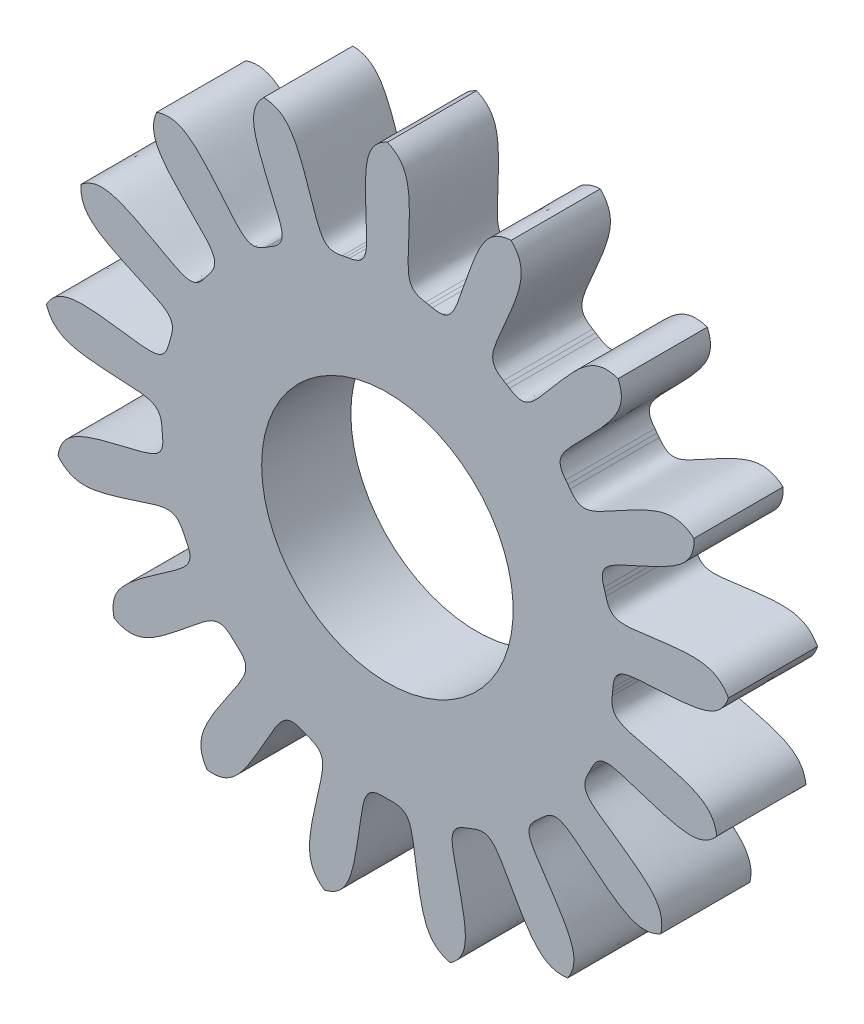
SolidWorks part; units mm, degrees
ref_plane "Alzado" through (0, 0, 0) normal (0, 0, 1) x (1, 0, 0)
ref_plane "Planta" through (0, 0, 0) normal (0, 1, 0) x (1, 0, 0)
ref_plane "Vista lateral" through (0, 0, 0) normal (1, 0, 0) x (0, 0, -1)
sketch "Sketch1" plane through (0, 0, 0) normal (0, 0, 1) x (1, 0, 0)
  line L0 (0, -1000) -> (0, 49000) construction
  line L1 (0, 0) -> (0.6543, 3.5) construction
  line L2 (0.2133, 1.2499) -> (0.233, 1.2464)
  line L3 (-0.2133, 1.2499) -> (-0.233, 1.2464)
  line L4 (0.2526, 1.2426) -> (0.233, 1.2464)
  line L5 (0.6504, 1.0885) -> (0.6675, 1.0781)
  line L6 (0.6844, 1.0674) -> (0.6675, 1.0781)
  line L7 (0.9997, 0.78) -> (1.0119, 0.7641)
  line L8 (1.0238, 0.7481) -> (1.0119, 0.7641)
  line L9 (1.214, 0.3662) -> (1.2196, 0.347)
  line L10 (1.2249, 0.3277) -> (1.2196, 0.347)
  line L11 (1.2643, -0.0971) -> (1.2626, -0.117)
  line L12 (1.2606, -0.1369) -> (1.2626, -0.117)
  line L13 (1.1438, -0.5472) -> (1.1351, -0.5652)
  line L14 (1.126, -0.583) -> (1.1351, -0.5652)
  line L15 (0.8689, -0.9235) -> (0.8542, -0.9371)
  line L16 (0.8394, -0.9504) -> (0.8542, -0.9371)
  line L17 (0.4766, -1.175) -> (0.4581, -1.1824)
  line L18 (0.4393, -1.1895) -> (0.4581, -1.1824)
  line L19 (0.02, -1.2678) -> (0, -1.268)
  line L20 (-0.02, -1.2678) -> (0, -1.268)
  line L21 (-0.4393, -1.1895) -> (-0.4581, -1.1824)
  line L22 (-0.4766, -1.175) -> (-0.4581, -1.1824)
  line L23 (-0.8394, -0.9504) -> (-0.8542, -0.9371)
  line L24 (-0.8689, -0.9235) -> (-0.8542, -0.9371)
  line L25 (-1.126, -0.583) -> (-1.1351, -0.5652)
  line L26 (-1.1438, -0.5472) -> (-1.1351, -0.5652)
  line L27 (-1.2606, -0.1369) -> (-1.2626, -0.117)
  line L28 (-1.2643, -0.0971) -> (-1.2626, -0.117)
  line L29 (-1.2249, 0.3277) -> (-1.2196, 0.347)
  line L30 (-1.214, 0.3662) -> (-1.2196, 0.347)
  line L31 (-1.0238, 0.7481) -> (-1.0119, 0.7641)
  line L32 (-0.9997, 0.78) -> (-1.0119, 0.7641)
  line L33 (-0.6844, 1.0674) -> (-0.6675, 1.0781)
  line L34 (-0.6504, 1.0885) -> (-0.6675, 1.0781)
  line L35 (-0.2526, 1.2426) -> (-0.233, 1.2464)
  circle A0 centre (0, 0) radius 1.92 construction
  circle A1 centre (0, 0) radius 1.268 construction
  spline S0 degree 3 poles (0, 1.92) (0.1051, 1.8729) (0.1297, 1.764) (0.1133, 1.3379) (0.1067, 1.2671) (0.2133, 1.2499) knots 0 0 0 0 0.42728 0.52728 1 1 1 1
  spline S1 degree 3 poles (0, 1.92) (-0.1051, 1.8729) (-0.1297, 1.764) (-0.1133, 1.3379) (-0.1067, 1.2671) (-0.2133, 1.2499) knots 0 0 0 0 0.42728 0.52728 1 1 1 1
  spline S2 degree 3 poles (0.6936, 1.7903) (0.5786, 1.7844) (0.5163, 1.6917) (0.3776, 1.2885) (0.3583, 1.2201) (0.2526, 1.2426) knots 0 0 0 0 0.42728 0.52728 1 1 1 1
  spline S3 degree 3 poles (0.6936, 1.7903) (0.7746, 1.7084) (0.7581, 1.598) (0.589, 1.2066) (0.5572, 1.143) (0.6504, 1.0885) knots 0 0 0 0 0.42728 0.52728 1 1 1 1
  spline S4 degree 3 poles (1.2935, 1.4189) (1.1841, 1.4549) (1.0926, 1.391) (0.8175, 1.065) (0.7748, 1.0083) (0.6844, 1.0674) knots 0 0 0 0 0.42728 0.52728 1 1 1 1
  spline S5 degree 3 poles (1.2935, 1.4189) (1.3394, 1.3133) (1.2842, 1.2163) (0.9851, 0.9123) (0.9325, 0.8646) (0.9997, 0.78) knots 0 0 0 0 0.42728 0.52728 1 1 1 1
  spline S6 degree 3 poles (1.7187, 0.8558) (1.6297, 0.9289) (1.5213, 0.9023) (1.1471, 0.6978) (1.0867, 0.6603) (1.0238, 0.7481) knots 0 0 0 0 0.42728 0.52728 1 1 1 1
  spline S7 degree 3 poles (1.7187, 0.8558) (1.7234, 0.7407) (1.6369, 0.6702) (1.2481, 0.4949) (1.1819, 0.4693) (1.214, 0.3662) knots 0 0 0 0 0.42728 0.52728 1 1 1 1
  spline S8 degree 3 poles (1.9118, 0.1772) (1.8552, 0.2775) (1.7445, 0.2919) (1.3217, 0.2363) (1.2519, 0.2232) (1.2249, 0.3277) knots 0 0 0 0 0.42728 0.52728 1 1 1 1
  spline S9 degree 3 poles (1.9118, 0.1772) (1.8746, 0.0682) (1.7684, 0.0337) (1.3426, 0.0106) (1.2716, 0.0107) (1.2643, -0.0971) knots 0 0 0 0 0.42728 0.52728 1 1 1 1
  spline S10 degree 3 poles (1.8467, -0.5254) (1.8301, -0.4115) (1.7321, -0.358) (1.3178, -0.2571) (1.248, -0.2441) (1.2606, -0.1369) knots 0 0 0 0 0.42728 0.52728 1 1 1 1
  spline S11 degree 3 poles (1.8467, -0.5254) (1.7726, -0.6136) (1.6612, -0.6074) (1.2558, -0.4751) (1.1896, -0.4494) (1.1438, -0.5472) knots 0 0 0 0 0.42728 0.52728 1 1 1 1
  spline S12 degree 3 poles (1.5322, -1.1571) (1.5579, -1.0448) (1.4858, -0.9596) (1.1359, -0.7158) (1.0755, -0.6785) (1.126, -0.583) knots 0 0 0 0 0.42728 0.52728 1 1 1 1
  spline S13 degree 3 poles (1.5322, -1.1571) (1.4312, -1.2125) (1.3296, -1.1665) (0.9993, -0.8967) (0.9469, -0.8488) (0.8689, -0.9235) knots 0 0 0 0 0.42728 0.52728 1 1 1 1
  spline S14 degree 3 poles (1.0107, -1.6324) (1.0753, -1.537) (1.0389, -1.4315) (0.8007, -1.0778) (0.7578, -1.0212) (0.8394, -0.9504) knots 0 0 0 0 0.42728 0.52728 1 1 1 1
  spline S15 degree 3 poles (1.0107, -1.6324) (0.8966, -1.6477) (0.8184, -1.568) (0.6079, -1.1971) (0.5764, -1.1335) (0.4766, -1.175) knots 0 0 0 0 0.42728 0.52728 1 1 1 1
  spline S16 degree 3 poles (0.3528, -1.8873) (0.4474, -1.8217) (0.4516, -1.7101) (0.3572, -1.2942) (0.3377, -1.226) (0.4393, -1.1895) knots 0 0 0 0 0.42728 0.52728 1 1 1 1
  spline S17 degree 3 poles (0.3528, -1.8873) (0.2408, -1.8603) (0.1967, -1.7578) (0.1344, -1.3359) (0.128, -1.2652) (0.02, -1.2678) knots 0 0 0 0 0.42728 0.52728 1 1 1 1
  spline S18 degree 3 poles (-0.3528, -1.8873) (-0.2408, -1.8603) (-0.1967, -1.7578) (-0.1344, -1.3359) (-0.128, -1.2652) (-0.02, -1.2678) knots 0 0 0 0 0.42728 0.52728 1 1 1 1
  spline S19 degree 3 poles (-0.3528, -1.8873) (-0.4474, -1.8217) (-0.4516, -1.7101) (-0.3572, -1.2942) (-0.3377, -1.226) (-0.4393, -1.1895) knots 0 0 0 0 0.42728 0.52728 1 1 1 1
  spline S20 degree 3 poles (-1.0107, -1.6324) (-0.8966, -1.6477) (-0.8184, -1.568) (-0.6079, -1.1971) (-0.5764, -1.1335) (-0.4766, -1.175) knots 0 0 0 0 0.42728 0.52728 1 1 1 1
  spline S21 degree 3 poles (-1.0107, -1.6324) (-1.0753, -1.537) (-1.0389, -1.4315) (-0.8007, -1.0778) (-0.7578, -1.0212) (-0.8394, -0.9504) knots 0 0 0 0 0.42728 0.52728 1 1 1 1
  spline S22 degree 3 poles (-1.5322, -1.1571) (-1.4312, -1.2125) (-1.3296, -1.1665) (-0.9993, -0.8967) (-0.9469, -0.8488) (-0.8689, -0.9235) knots 0 0 0 0 0.42728 0.52728 1 1 1 1
  spline S23 degree 3 poles (-1.5322, -1.1571) (-1.5579, -1.0448) (-1.4858, -0.9596) (-1.1359, -0.7158) (-1.0755, -0.6785) (-1.126, -0.583) knots 0 0 0 0 0.42728 0.52728 1 1 1 1
  spline S24 degree 3 poles (-1.8467, -0.5254) (-1.7726, -0.6136) (-1.6612, -0.6074) (-1.2558, -0.4751) (-1.1896, -0.4494) (-1.1438, -0.5472) knots 0 0 0 0 0.42728 0.52728 1 1 1 1
  spline S25 degree 3 poles (-1.8467, -0.5254) (-1.8301, -0.4115) (-1.7321, -0.358) (-1.3178, -0.2571) (-1.248, -0.2441) (-1.2606, -0.1369) knots 0 0 0 0 0.42728 0.52728 1 1 1 1
  spline S26 degree 3 poles (-1.9118, 0.1772) (-1.8746, 0.0682) (-1.7684, 0.0337) (-1.3426, 0.0106) (-1.2716, 0.0107) (-1.2643, -0.0971) knots 0 0 0 0 0.42728 0.52728 1 1 1 1
  spline S27 degree 3 poles (-1.9118, 0.1772) (-1.8552, 0.2775) (-1.7445, 0.2919) (-1.3217, 0.2363) (-1.2519, 0.2232) (-1.2249, 0.3277) knots 0 0 0 0 0.42728 0.52728 1 1 1 1
  spline S28 degree 3 poles (-1.7187, 0.8558) (-1.7234, 0.7407) (-1.6369, 0.6702) (-1.2481, 0.4949) (-1.1819, 0.4693) (-1.214, 0.3662) knots 0 0 0 0 0.42728 0.52728 1 1 1 1
  spline S29 degree 3 poles (-1.7187, 0.8558) (-1.6297, 0.9289) (-1.5213, 0.9023) (-1.1471, 0.6978) (-1.0867, 0.6603) (-1.0238, 0.7481) knots 0 0 0 0 0.42728 0.52728 1 1 1 1
  spline S30 degree 3 poles (-1.2935, 1.4189) (-1.3394, 1.3133) (-1.2842, 1.2163) (-0.9851, 0.9123) (-0.9325, 0.8646) (-0.9997, 0.78) knots 0 0 0 0 0.42728 0.52728 1 1 1 1
  spline S31 degree 3 poles (-1.2935, 1.4189) (-1.1841, 1.4549) (-1.0926, 1.391) (-0.8175, 1.065) (-0.7748, 1.0083) (-0.6844, 1.0674) knots 0 0 0 0 0.42728 0.52728 1 1 1 1
  spline S32 degree 3 poles (-0.6936, 1.7903) (-0.7746, 1.7084) (-0.7581, 1.598) (-0.589, 1.2066) (-0.5572, 1.143) (-0.6504, 1.0885) knots 0 0 0 0 0.42728 0.52728 1 1 1 1
  spline S33 degree 3 poles (-0.6936, 1.7903) (-0.5786, 1.7844) (-0.5163, 1.6917) (-0.3776, 1.2885) (-0.3583, 1.2201) (-0.2526, 1.2426) knots 0 0 0 0 0.42728 0.52728 1 1 1 1
  point P4 (0, 1.92)
  point P8 (0.233, 1.2464)
  point P9 (0.2133, 1.2499)
  point P132 (0, 0)
  dimension "D1" = 3.84
  dimension "D2" = 2.536
  dimension "D3" = 10.588
  dimension "D4" = 0.02
  dimension "D5" = 17
extrude "Boss-Extrude1 (17 teeth)" add sketch "Sketch1" along normal blind 0.5
sketch "Sketch2" plane through (0, 0, 0) normal (0, 0, 1) x (1, 0, 0)
  circle A0 centre (0, 0) radius 0.705
  dimension "D1" = 1.41
extrude "Cut-Extrude1" cut sketch "Sketch2" along normal up to next
